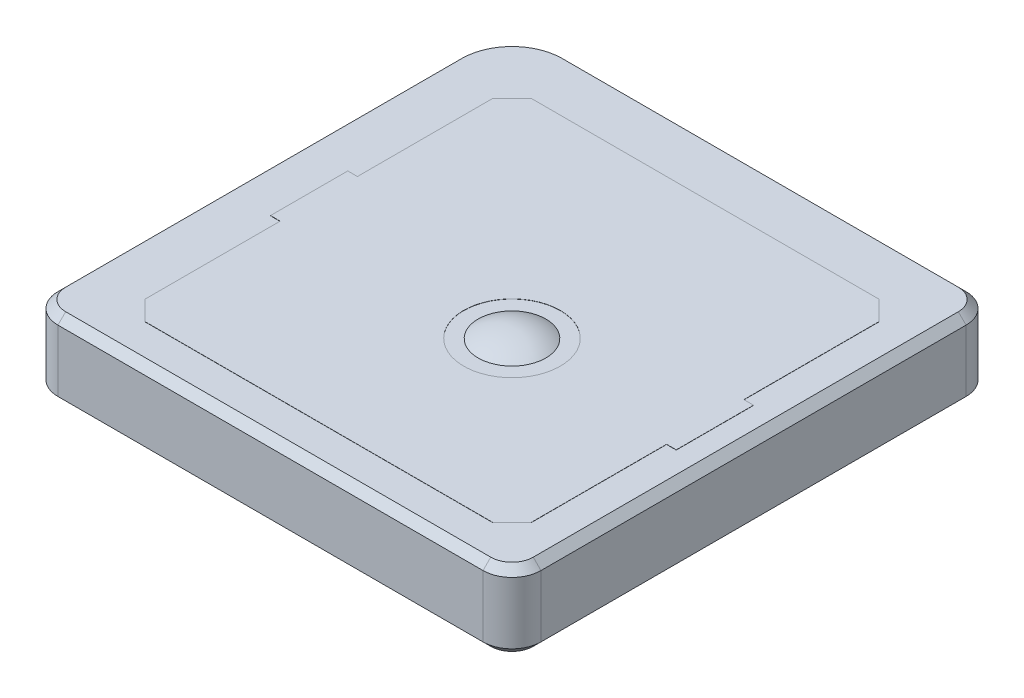
SolidWorks part; units mm, degrees
ref_plane "Front Plane" through (0, 0, 0) normal (0, 0, 1) x (1, 0, 0)
ref_plane "Top Plane" through (0, 0, 0) normal (0, 1, 0) x (1, 0, 0)
ref_plane "Right Plane" through (0, 0, 0) normal (1, 0, 0) x (0, 0, -1)
sketch "Sketch1" plane through (0, 0, 0) normal (0, 1, 0) x (1, 0, 0)
  line L1 (-12.75, -10.75) -> (9.25, -10.75)
  line L2 (-14.25, -9.25) -> (-14.25, 11.25)
  line L3 (-11.25, 14.25) -> (9.25, 14.25)
  line L4 (10.75, -9.25) -> (10.75, 12.75)
  line L5 (-14.25, -10.75) -> (10.75, 14.25) construction
  line L6 (-14.25, 14.25) -> (10.75, -10.75) construction
  arc A0 (-14.25, 11.25) -> (-11.25, 14.25) centre (-11.25, 11.25) cw
  arc A1 (9.25, 14.25) -> (10.75, 12.75) centre (9.25, 12.75) cw
  arc A2 (10.75, -9.25) -> (9.25, -10.75) centre (9.25, -9.25) cw
  arc A3 (-12.75, -10.75) -> (-14.25, -9.25) centre (-12.75, -9.25) cw
  point P0 (-1.75, 1.75)
  dimension "D5" = 3
  dimension "D6" = 1.5
  dimension "D1" = 25
  dimension "D2" = 25
  dimension "D3" = 1.75
  dimension "D4" = 1.75
extrude "Boss-Extrude1" add sketch "Sketch1" along normal blind 4
chamfer "Chamfer1" distance 0.4 angle 45 16 edges at (-14.25, 0, -1) (-13.8107, 0, 10.3107) (-1.75, 0, 10.75) (10.3107, 0, 10.3107) (10.75, 0, -1.75) (10.3107, 0, -13.8107) (-1, 0, -14.25) (-13.3713, 0, -13.3713) (-1, 4, -14.25) (10.3107, 4, -13.8107) (10.75, 4, -1.75) (10.3107, 4, 10.3107) (-1.75, 4, 10.75) (-13.8107, 4, 10.3107) (-14.25, 4, -1) (-13.3713, 4, -13.3713)
sketch "Sketch2" plane through (0, 0, 0) normal (0, 0, 1) x (1, 0, 0)
  line L0 (0, 5.8921) -> (0, -4.4343) construction
  line L1 (-12.75, 4) -> (9.25, 4) construction
  line L2 (-3.2153, 1.9839) -> (-0.5, 1.9839)
  line L3 (-0.5, 1.9839) -> (-0.5, -2.4)
  line L4 (-0.5, -2.4) -> (0, -2.4)
  line L5 (9.25, 0) -> (-12.75, 0) construction
  line L6 (0, -2.4) -> (0, 4.5)
  arc A1 (0, 4.5) -> (-3.2153, 1.9839) centre (0, 1.1875) ccw
  point P5 (0, 4.5)
  point P6 (0, 4)
  point P7 (1.75, 4)
  point P10 (-1.75, 4)
  dimension "D1" = 0.5
  dimension "D2" = 3.5
  dimension "D3" = 0.5
  dimension "D4" = 2.4
revolve "Revolve1" add sketch "Sketch2" angle 360 about L0
sketch "Sketch3" plane through (0, 0, 0) normal (0, 1, 0) x (1, 0, 0)
  line L0 (-14.25, -9.25) -> (-14.25, 11.25) construction
  line L1 (-10.25, 11.25) -> (7.75, 11.25)
  line L2 (-11.25, 10.25) -> (-11.25, 3.25)
  line L3 (-10.25, -8.75) -> (7.75, -8.75)
  line L4 (8.75, 10.25) -> (8.75, 3.25)
  line L5 (-11.25, 14.25) -> (9.25, 14.25) construction
  line L6 (-11.25, 10.25) -> (-10.25, 11.25)
  line L7 (-11.25, -7.75) -> (-10.25, -8.75)
  line L8 (7.75, -8.75) -> (8.75, -7.75)
  line L9 (7.75, 11.25) -> (8.75, 10.25)
  line L10 (-11.25, 3.25) -> (-11.75, 3.25)
  line L11 (-11.75, 3.25) -> (-11.75, -0.75)
  line L12 (-11.75, -0.75) -> (-11.25, -0.75)
  line L13 (-11.25, -0.75) -> (-11.25, -7.75)
  line L14 (8.75, 3.25) -> (9.25, 3.25)
  line L15 (9.25, 3.25) -> (9.25, -0.75)
  line L16 (9.25, -0.75) -> (8.75, -0.75)
  line L17 (8.75, -0.75) -> (8.75, -7.75)
  circle A0 centre (0, 0) radius 2.5
  point P0 (-11.25, 11.25)
  point P1 (8.75, -8.75)
  point P2 (-11.25, -8.75)
  point P3 (8.75, 11.25)
  dimension "D5" = 5
  dimension "D1" = 20
  dimension "D2" = 20
  dimension "D3" = 3
  dimension "D4" = 3
  dimension "D6" = 4
  dimension "D11" = 0.5
  dimension "D12" = 0.5
  dimension "D13" = 4
extrude "Boss-Extrude2" add sketch "Sketch3" along normal blind 0.01 from surface at 4 starting at face at (0, 4, -1.75)
